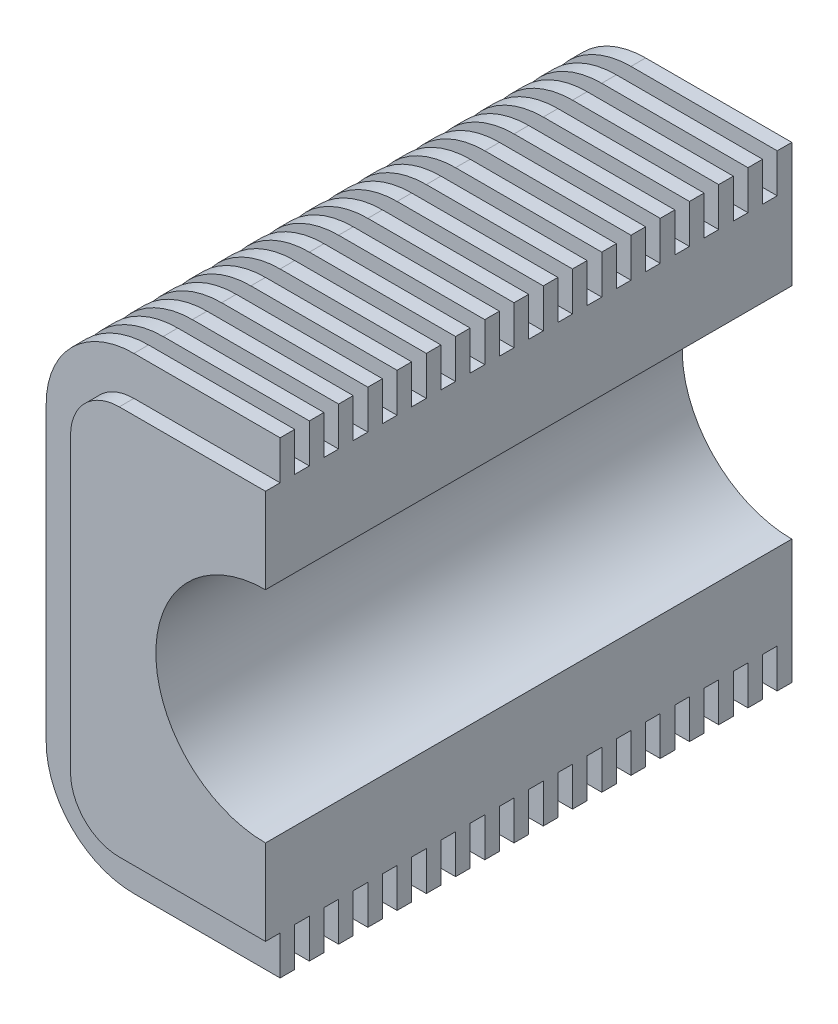
SolidWorks part; units mm, degrees
ref_plane "Płaszczyzna przednia" through (0, 0, 0) normal (0, 0, 1) x (1, 0, 0)
ref_plane "Płaszczyzna górna" through (0, 0, 0) normal (0, 1, 0) x (1, 0, 0)
ref_plane "Płaszczyzna prawa" through (0, 0, 0) normal (1, 0, 0) x (0, 0, -1)
sketch "Szkic1" plane through (0, 0, 0) normal (0, 0, 1) x (1, 0, 0)
  line L0 (0, 75) -> (-30, 75) construction
  line L1 (-40, 5) -> (-40, 65) construction
  line L2 (0, -5) -> (-30, -5) construction
  line L3 (0, 75) -> (-30, 75)
  line L4 (-40, 5) -> (-40, 65)
  line L5 (0, -5) -> (-30, -5)
  line L6 (0, -5) -> (0, 75)
  arc A0 (-30, 75) -> (-40, 65) centre (-30, 65) ccw construction
  arc A1 (-40, 5) -> (-30, -5) centre (-30, 5) ccw construction
  arc A2 (-30, 75) -> (-40, 65) centre (-30, 65) ccw
  arc A3 (-40, 5) -> (-30, -5) centre (-30, 5) ccw
extrude "Dodanie-wyciągnięcie1" add sketch "Szkic1" along normal blind 108
sketch "Szkic2" plane through (0, 0, 108) normal (0, 0, 1) x (1, 0, 0)
  circle A1 centre (0, 35) radius 22.5 construction
  circle A2 centre (0, 35) radius 22.5
sketch "Szkic3" plane through (0, 0, 0) normal (0, 0, -1) x (-1, 0, 0)
  line L0 (0, 75) -> (30, 75) construction
  line L1 (40, 65) -> (40, 5) construction
  line L2 (30, -5) -> (0, -5) construction
  line L3 (0, 75) -> (30, 75)
  line L4 (40, 65) -> (40, 5)
  line L5 (30, -5) -> (0, -5)
  line L6 (0, 83) -> (30, 83)
  line L7 (48, 65) -> (48, 5)
  line L8 (30, -13) -> (0, -13)
  line L9 (0, -13) -> (0, -5)
  line L10 (0, 75) -> (0, 83)
  arc A0 (40, 65) -> (30, 75) centre (30, 65) ccw construction
  arc A1 (30, -5) -> (40, 5) centre (30, 5) ccw construction
  arc A2 (40, 65) -> (30, 75) centre (30, 65) ccw
  arc A3 (30, -5) -> (40, 5) centre (30, 5) ccw
  arc A4 (48, 65) -> (30, 83) centre (30, 65) ccw
  arc A5 (30, -13) -> (48, 5) centre (30, 5) ccw
  dimension "D1" = 8
extrude "Dodanie-wyciągnięcie2" add sketch "Szkic3" against normal blind 3
pattern_linear "Szyk liniowy2" count 18 spacing 6 along (0, 0, 1) of "Dodanie-wyciągnięcie2"
extrude "Wytnij-wyciągnięcie1" cut sketch "Szkic2" against normal through all
